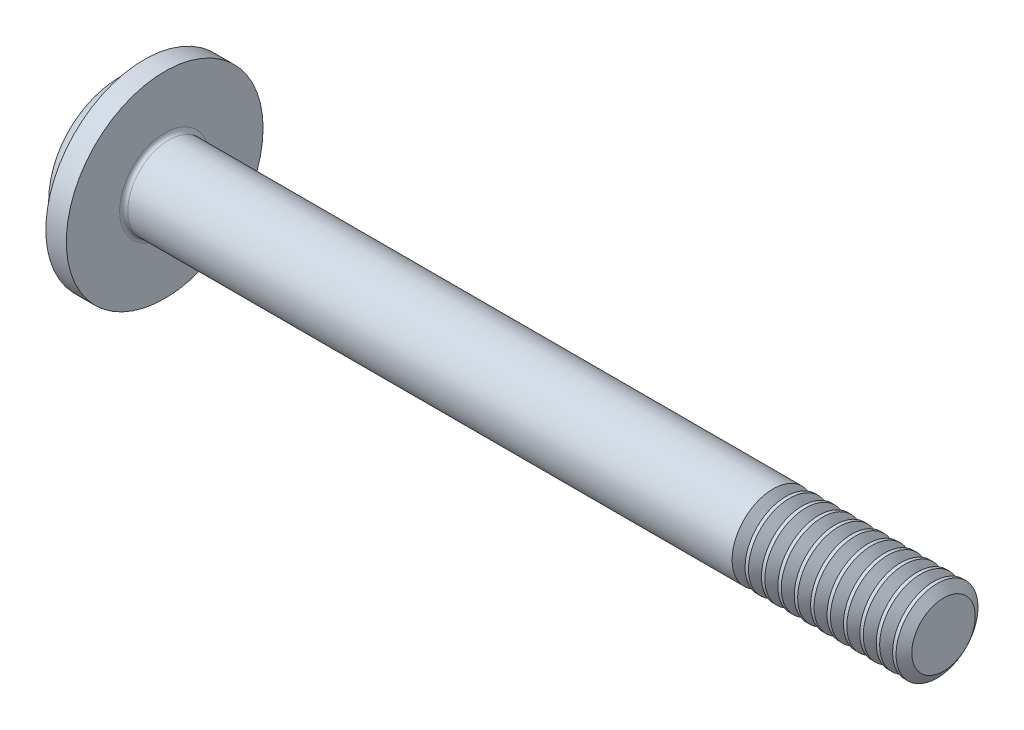
SolidWorks part; units mm, degrees
material "Aço NB 1045"
ref_plane "Plane1" through (0, 0, 0) normal (0, 0, 1) x (1, 0, 0)
ref_plane "Plane2" through (0, 0, 0) normal (0, 1, 0) x (1, 0, 0)
ref_plane "Plane3" through (0, 0, 0) normal (1, 0, 0) x (0, 0, -1)
sketch "BodySke" plane through (0, 0, 0) normal (0, 0, 1) x (1, 0, 0)
  line L0 (1.6, 1) -> (1.6, 2)
  line L1 (1.8, 6.35) -> (1.8, -3.175) construction
  line L2 (-25.4, 0) -> (127, 0) construction
  line L3 (20.6, 0) -> (0, 0)
  line L4 (1.6, 1) -> (20.6, 1)
  line L5 (20.6, 1) -> (20.6, 0)
  line L6 (1.1, 2) -> (1.6, 2)
  line L8 (16.6, 6.35) -> (16.6, -3.175) construction
  arc A0 (0.3941, 1.5765) -> (0, 0) centre (3.35, 0) ccw
  arc A2 (0.3941, 1.5765) -> (1.1, 2) centre (1.1, 1.2) cw
  dimension "D2" = 0.8
  dimension "Length" = 19
  dimension "Head_ht" = 1.6
  dimension "Head_dia" = 4
  dimension "Advance" = 0.4
  dimension "Thread_nom" = 4
  dimension "Diameter" = 2
  dimension "D1" = 0.5
revolve "Base-Revolve" add sketch "BodySke"
cosmetic thread "ThreadCosmetic" [suppressed]
fillet "Fillet1" radius 0.1 1 edges at (1.6, 0, 1)
sketch "Sketch3" plane through (0, 0, 0) normal (1, 0, 0) x (0, 0, -1)
  line L0 (0.24, -1.05) -> (-0.24, -1.05)
  line L1 (0.24, -1.05) -> (0.24, 1.05)
  line L2 (-0.24, 1.05) -> (0.24, 1.05)
  line L3 (-0.24, 1.05) -> (-0.24, -1.05)
  dimension "Cross_dia" = 2.1
  dimension "D1" = 1.05
  dimension "Cross_width" = 0.48
  dimension "D2" = 0.24
ref_plane "Plane4" through (1.42, 0, 0) normal (1, 0, 0) x (0, 0, -1)
sketch "Sketch4" plane through (1.42, 0, 0) normal (1, 0, 0) x (0, 0, -1)
  line L0 (0.24, -0.342) -> (-0.24, -0.342)
  line L1 (0.24, -0.342) -> (0.24, 0.342)
  line L2 (-0.24, 0.342) -> (0.24, 0.342)
  line L3 (-0.24, 0.342) -> (-0.24, -0.342)
  dimension "D1" = 0.48
  dimension "D2" = 0.684
  dimension "D3" = 0.24
  dimension "D4" = 0.342
loft "Recess" cut profiles "Sketch3", "Sketch4"
pattern_circular "RecPat" count 2 every 90 about axis through (0, 0, 0) along (1, 0, 0) of "Recess"
sketch "RecCorSke" plane through (0, 0, 0) normal (0, 0, 1) x (1, 0, 0)
  line L0 (-3.175, 0) -> (15.875, 0) construction
  line L1 (-25.4, 0) -> (127, 0) construction
  line L2 (0, 0) -> (0, 0.4548)
  line L3 (0, 0.4548) -> (1.42, 0.3555)
  line L4 (1.42, 0.3555) -> (1.5355, 0)
  line L5 (1.5355, 0) -> (0, 0)
  dimension "Diameter" = 0.711
  dimension "Depth" = 1.42
  dimension "Draft_angle" = 4
  dimension "Bottom_angle" = 18
revolve "RecessCore" cut sketch "RecCorSke" angle 360 about L0
sketch "ThdSchSke" plane through (0, 0, 0) normal (0, 0, 1) x (1, 0, 0)
  line L0 (16.6, -0.774) -> (16.4418, -1)
  line L1 (16.6, -0.774) -> (16.7582, -1)
  line L2 (16.7582, -1) -> (16.7582, -1.25)
  line L3 (-3.175, 0) -> (5.1513, 0) construction
  line L5 (16.7582, -1.25) -> (16.4418, -1.25)
  line L6 (16.4418, -1.25) -> (16.4418, -1)
  dimension "Diameter" = 2
  dimension "SideAngle" = 55
  dimension "VeeAngle" = 70
  dimension "Thread_minor" = 1.548
  dimension "Overcut" = 2.5
  dimension "Start" = 16.6
revolve "ThreadSchematic" cut sketch "ThdSchSke" angle 360 about L3
pattern_linear "ThdSchPat" count 11 spacing 0.4 along (1, 0, 0) of "ThreadSchematic"
sketch "Esboço1" plane through (1.6, 0, 0) normal (1, 0, 0) x (0, 0, -1)
  circle A0 centre (0, 0) radius 2.4
  dimension "D1" = 4.8
extrude "Ressalto-extrusão1" add sketch "Esboço1" against normal blind 0.5
sketch "Esboço2" plane through (0, 0, 0) normal (0, 1, 0) x (1, 0, 0)
  line L0 (0, 0) -> (9.6, 0) construction
  line L1 (9.6, -0.774) -> (9.6, 0.774) construction
  line L2 (9.6, 0.3) -> (8.1, 1)
  line L4 (8.1, 1) -> (9.6, 1)
  line L5 (9.6, 1) -> (9.6, 0.3)
  line L6 (7.5813, 1) -> (7.5024, 1) construction
  dimension "D1" = 1.5
  dimension "D2" = 0.6
equation "\"D1@Sketch3\" = \"Cross_dia@Sketch3\" / 2"
equation "\"D2@Sketch3\" = \"Cross_width@Sketch3\" / 2"
equation "\"Depth@RecCorSke\" = \"Cross_depth@Plane4\""
equation "\"D1@Sketch4\" = \"Cross_width@Sketch3\""
equation "\"D2@Sketch4\" = \"Cross_dia@Sketch3\" - 2.0 * \"Cross_depth@Plane4\" * tan(26.5  * 0.017453292)"
equation "\"D3@Sketch4\" = \"D1@Sketch4\" / 2"
equation "\"D4@Sketch4\" = \"D2@Sketch4\" / 2"
equation "\"Thread_length@ThreadCosmetic\" = ((sgn( (\"Length@BodySke\" - \"Advance@BodySke\" * 2.0 ) - \"Thread_nom@BodySke\" )-1)*( (\"Length@BodySke\" - \"Advance@BodySke\" * 2.0 ) - \"Thread_nom@BodySke\" ))/-2+ \"Thread_nom@BodySke\""
equation "\"Thread_minor@ThdSchSke\" = \"Thread_minor@ThreadCosmetic\""
equation "\"Diameter@ThdSchSke\" = \"Diameter@BodySke\""
equation "\"Overcut@ThdSchSke\" = \"Diameter@BodySke\" * 1.25"
equation "\"Start@ThdSchSke\" = \"Head_ht@BodySke\" + \"Length@BodySke\" - \"Thread_length@ThreadCosmetic\"  '---Non-countersunk---"
equation "\"Num_threads@ThdSchPat\" = int( \"Thread_length@ThreadCosmetic\" / \"Advance@BodySke\" + 0.999 )  + 1"
equation "\"Advance@ThdSchPat\" = \"Thread_length@ThreadCosmetic\" /  (\"Num_threads@ThdSchPat\" - 1) 'relax it"
